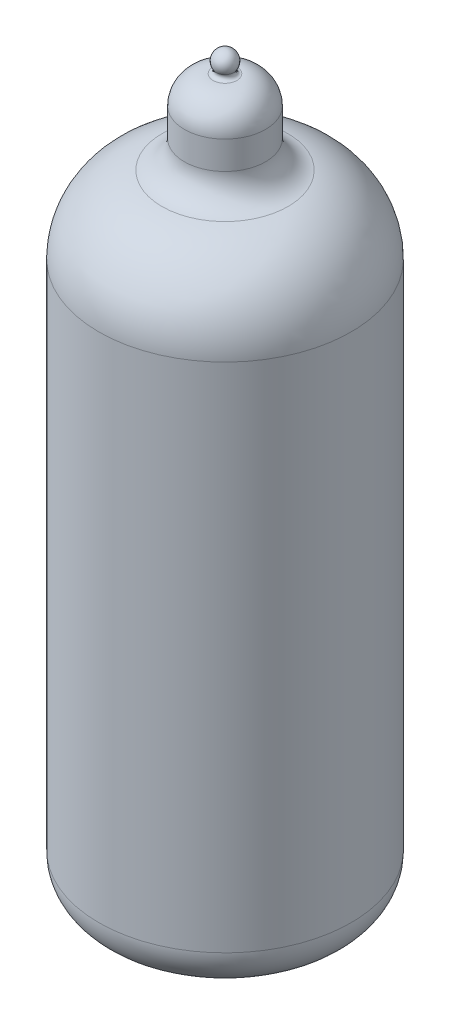
SolidWorks part; units mm, degrees
material "Glass"
ref_plane "Front Plane" through (0, 0, 0) normal (0, 0, 1) x (1, 0, 0)
ref_plane "Top Plane" through (0, 0, 0) normal (0, 1, 0) x (1, 0, 0)
ref_plane "Right Plane" through (0, 0, 0) normal (1, 0, 0) x (0, 0, -1)
sketch "Sketch1" plane through (0, 0, 0) normal (0, 0, 1) x (1, 0, 0)
  line L0 (0, 26.25) -> (0, -26.25) construction
  line L1 (0, -26.25) -> (-6, -26.25)
  line L2 (-9, -23.25) -> (-9, 13.25)
  line L3 (-2.896, 20.7104) -> (-2.896, 22.7104)
  line L4 (-7.5, -22.25) -> (0, -22.25)
  line L5 (-8.5, -21.25) -> (-8.5, 13.25)
  line L6 (-2.396, 20.7104) -> (-2.396, 22.7104)
  line L7 (-0.896, 24.2104) -> (0, 24.2104)
  line L8 (0, 26.25) -> (0, 24.2104)
  line L9 (0, -22.25) -> (0, -26.25)
  line L10 (0, -25.75) -> (-6, -25.75) construction
  line L12 (-8.5, -23.25) -> (-8.5, 13.25) construction
  arc A0 (-6, -26.25) -> (-9, -23.25) centre (-6, -23.25) cw
  arc A1 (-9, 13.25) -> (-4.5, 18.75) centre (-3.3889, 13.25) cw
  arc A2 (-4.5, 18.75) -> (-2.896, 20.7104) centre (-4.896, 20.7104) ccw
  arc A3 (-2.896, 22.7104) -> (-0.8476, 24.7098) centre (-0.896, 22.7104) cw
  arc A4 (-0.8476, 24.7098) -> (-0.6311, 25.0948) centre (-0.8415, 24.9597) ccw
  arc A5 (-0.6311, 25.0948) -> (0, 26.25) centre (0, 25.5) cw
  arc A6 (-7.5, -22.25) -> (-8.5, -21.25) centre (-7.5, -21.25) cw
  arc A7 (-8.5, 13.25) -> (-4.401, 18.2599) centre (-3.3889, 13.25) cw
  arc A8 (-4.401, 18.2599) -> (-2.396, 20.7104) centre (-4.896, 20.7104) ccw
  arc A9 (-2.396, 22.7104) -> (-0.896, 24.2104) centre (-0.896, 22.7104) cw
  arc A12 (-0.8597, 24.21) -> (-0.2104, 25.3649) centre (-0.8415, 24.9597) ccw construction
  arc A13 (-0.2104, 25.3649) -> (0, 25.75) centre (0, 25.5) cw construction
  arc A14 (-2.396, 22.7104) -> (-0.8597, 24.21) centre (-0.896, 22.7104) cw construction
  arc A15 (-6, -25.75) -> (-8.5, -23.25) centre (-6, -23.25) cw construction
  dimension "D2" = 3
  dimension "D3" = 18
  dimension "D6" = 2
  dimension "D8" = 2
  dimension "D9" = 0.75
  dimension "D11" = 0.25
  dimension "D13" = 4
  dimension "D14" = 1
  dimension "D1" = 52.5
  dimension "D4" = 9
  dimension "D5" = 5.5
  dimension "D7" = 2
  dimension "D10" = 7.5
  dimension "D12" = 0.5
revolve "Revolve1" add sketch "Sketch1" angle 360 about L0
sketch "Sketch2" plane through (0, -26.25, 0) normal (0, -1, 0) x (1, 0, 0)
  circle A0 centre (0, 0) radius 5.75 construction
  circle A1 centre (0, -5.75) radius 0.25
  circle A2 centre (-2.6722, -5.0914) radius 0.25
  circle A3 centre (-4.7322, -3.2664) radius 0.25
  circle A4 centre (-5.7081, -0.6931) radius 0.25
  circle A5 centre (-5.3763, 2.039) radius 0.25
  circle A6 centre (-3.813, 4.3039) radius 0.25
  circle A7 centre (-1.3761, 5.5829) radius 0.25
  circle A8 centre (1.3761, 5.5829) radius 0.25
  circle A9 centre (3.813, 4.3039) radius 0.25
  circle A10 centre (5.3763, 2.039) radius 0.25
  circle A11 centre (5.7081, -0.6931) radius 0.25
  circle A12 centre (4.7322, -3.2664) radius 0.25
  circle A13 centre (2.6722, -5.0914) radius 0.25
  point P32 (0, 0)
  dimension "D1" = 11.5
  dimension "D2" = 0.5
  dimension "D3" = 13
extrude "Cut-Extrude1" cut sketch "Sketch2" against normal up to next
sketch "Sketch3" plane through (0, -26.25, 0) normal (0, -1, 0) x (1, 0, 0)
  line L1 (0.375, -2.5) -> (-0.375, -2.5) construction
  line L2 (0.375, -2.5) -> (0.375, 2.5) construction
  line L3 (0.375, 2.5) -> (-0.375, 2.5)
  line L4 (-0.375, -2.5) -> (-0.375, 2.5) construction
  line L5 (0.375, -2.5) -> (-0.375, 2.5) construction
  line L6 (0.375, 2.5) -> (-0.375, -2.5) construction
  line L7 (0, -2.5) -> (-0.75, -0.75)
  line L8 (-0.75, -0.75) -> (-0.375, -0.75)
  line L9 (-0.375, -0.75) -> (-0.375, 2.5)
  line L10 (0, -2.5) -> (0.75, -0.75)
  line L11 (0.75, -0.75) -> (0.375, -0.75)
  line L12 (0.375, -0.75) -> (0.375, 2.5)
  circle A0 centre (0, 0) radius 3
  dimension "D1" = 6
  dimension "D2" = 5
  dimension "D3" = 0.75
  dimension "D4" = 1.5
  dimension "D5" = 1.75
extrude "Cut-Extrude2" cut sketch "Sketch3" against normal blind 0.5 draft 15
